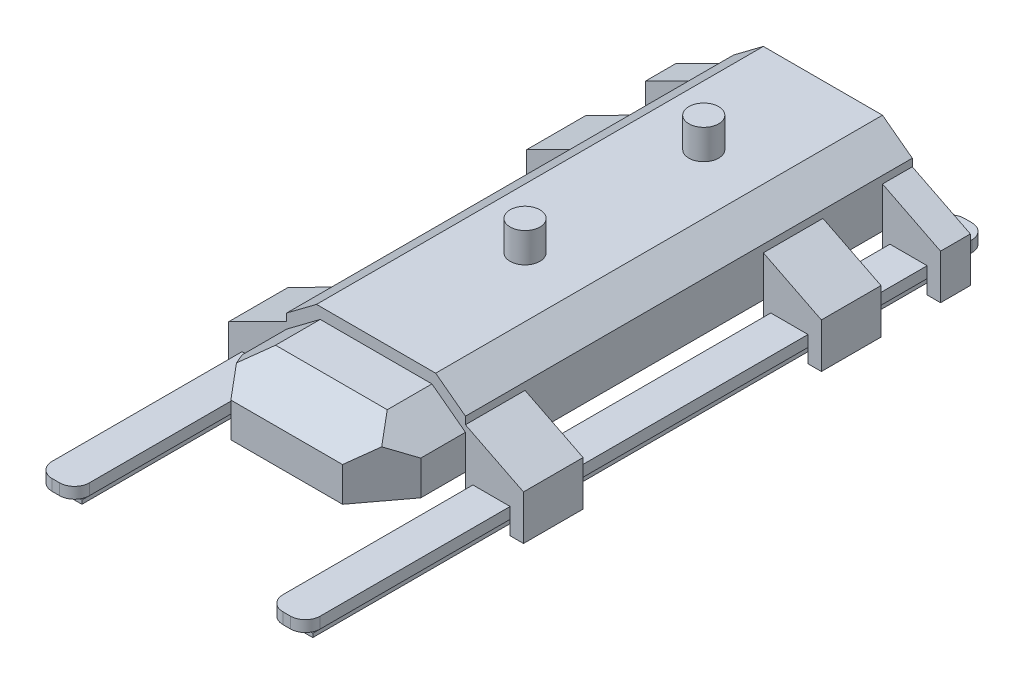
SolidWorks part; units mm, degrees
ref_plane "Front Plane" through (0, 0, 0) normal (0, 0, 1) x (1, 0, 0)
ref_plane "Top Plane" through (0, 0, 0) normal (0, 1, 0) x (1, 0, 0)
ref_plane "Right Plane" through (0, 0, 0) normal (1, 0, 0) x (0, 0, -1)
sketch "Sketch2" plane through (0, 0, 0) normal (0, 0, 1) x (1, 0, 0)
  line L0 (152.4, 0) -> (0, 0)
  line L1 (0, 0) -> (0, 120.65)
  line L2 (0, 120.65) -> (101.6, 120.65)
  line L3 (101.6, 120.65) -> (152.4, 82.55)
  line L4 (152.4, 82.55) -> (152.4, 69.85)
  line L5 (152.4, 0) -> (152.4, -50.8)
  line L6 (152.4, -50.8) -> (165.1, -50.8)
  line L7 (165.1, -50.8) -> (165.1, -12.7)
  line L8 (165.1, -12.7) -> (228.6, -12.7)
  line L9 (228.6, -12.7) -> (228.6, -56.0384)
  line L10 (228.6, -56.0384) -> (251.388, -56.0384)
  line L11 (251.388, -56.0384) -> (251.388, 20.1616)
  line L12 (251.388, 20.1616) -> (152.4, 69.85)
  dimension "D1" = 120.65
  dimension "D2" = 101.6
  dimension "D3" = 50.8
  dimension "D4" = 38.1
  dimension "D5" = 12.7
  dimension "D6" = 152.4
  dimension "D7" = 50.8
  dimension "D8" = 12.7
  dimension "D9" = 63.5
  dimension "D10" = 38.1
  dimension "D11" = 76.2
extrude "Boss-Extrude1" add sketch "Sketch2" along normal mid plane 762
sketch "Sketch3" plane through (0, 0, 0) normal (0, 1, 0) x (1, 0, 0)
  line L0 (152.4, -381) -> (152.4, 381) construction
  line L1 (152.4, -279.4) -> (251.388, -279.4)
  line L2 (152.4, -279.4) -> (152.4, 127)
  line L3 (152.4, 127) -> (251.388, 127)
  line L4 (251.388, -279.4) -> (251.388, 127)
  line L5 (251.388, -381) -> (251.388, 381) construction
  line L6 (251.388, -381) -> (152.4, -381) construction
  line L7 (152.4, 228.6) -> (251.388, 228.6)
  line L8 (152.4, 228.6) -> (152.4, 330.2)
  line L9 (152.4, 330.2) -> (251.388, 330.2)
  line L10 (251.388, 228.6) -> (251.388, 330.2)
  line L11 (251.388, 381) -> (152.4, 381) construction
  dimension "D1" = 101.6
  dimension "D2" = 50.8
  dimension "D3" = 101.6
  dimension "D4" = 101.6
extrude "Cut-Extrude1" cut sketch "Sketch3" against normal through all both and the other way through all
sketch "Sketch4" plane through (0, 0, 381) normal (0, 0, 1) x (1, 0, 0)
  line L0 (152.4, 0) -> (0, 0)
  line L1 (0, 0) -> (152.4, 0) construction
  line L2 (0, 0) -> (0, 101.6)
  line L3 (0, 120.65) -> (0, 0) construction
  line L4 (0, 101.6) -> (95.25, 101.6)
  line L5 (95.25, 101.6) -> (152.4, 58.7375)
  line L6 (152.4, 58.7375) -> (152.4, 0)
  line L7 (101.6, 120.65) -> (0, 120.65) construction
  line L8 (152.4, 82.55) -> (101.6, 120.65) construction
  line L9 (152.4, 0) -> (152.4, -50.8) construction
  dimension "D1" = 19.05
  dimension "D2" = 19.05
extrude "Boss-Extrude2" add sketch "Sketch4" along normal blind 152.4
sketch "Sketch6" plane through (0, 0, 0) normal (1, 0, 0) x (0, 0, -1)
  line L0 (-533.4, 101.6) -> (-533.4, 58.7375)
  line L1 (-533.4, 58.7375) -> (-457.2, 101.6)
  line L2 (-533.4, 101.6) -> (-381, 101.6) construction
  line L3 (-457.2, 101.6) -> (-533.4, 101.6)
extrude "Cut-Extrude2" cut sketch "Sketch6" against normal through all and the other way through all contours L3 L0 L1
sketch "Sketch7" plane through (0, 0, 0) normal (0, 1, 0) x (1, 0, 0)
  line L0 (152.4, -533.4) -> (152.4, -457.2)
  line L1 (152.4, -533.4) -> (152.4, -381) construction
  line L2 (152.4, -457.2) -> (95.25, -533.4)
  line L3 (152.4, -533.4) -> (0, -533.4) construction
  line L4 (95.25, -533.4) -> (152.4, -533.4)
extrude "Cut-Extrude3" cut sketch "Sketch7" against normal through all both and the other way through all
mirror "Mirror1" about plane through (0, 0, 0) normal (1, 0, 0) of bodies 105
sketch "Sketch8" plane through (0, 0, 0) normal (0, 0, 1) x (1, 0, 0)
  line L0 (-165.1, -50.8) -> (-165.1, -12.7) construction
  line L1 (-228.6, -12.7) -> (-165.1, -12.7)
  line L2 (-228.6, -12.7) -> (-228.6, -31.75)
  line L3 (-228.6, -31.75) -> (-165.1, -31.75)
  line L4 (-165.1, -12.7) -> (-165.1, -31.75)
  line L5 (228.6, -12.7) -> (228.6, -56.0384) construction
  line L6 (165.1, -12.7) -> (228.6, -12.7)
  line L7 (165.1, -12.7) -> (165.1, -31.75)
  line L8 (165.1, -31.75) -> (228.6, -31.75)
  line L9 (228.6, -12.7) -> (228.6, -31.75)
  dimension "D1" = 19.05
extrude "Boss-Extrude3" add sketch "Sketch8" along normal offset from surface 196.85 and the other way offset from surface (431.8 mm away) 50.8 up to face at (0, 29.3687, 533.4) offset beyond the face yes other way up to face at (0, 4.9213, -381)
fillet "Fillet1" radius 25.4 8 edges at (-228.6, -22.225, -431.8) (-165.1, -22.225, -431.8) (165.1, -22.225, -431.8) (228.6, -22.225, -431.8) (-228.6, -22.225, 730.25) (-165.1, -22.225, 730.25) (165.1, -22.225, 730.25) (228.6, -22.225, 730.25)
sketch "Sketch9" plane through (0, 0, 0) normal (0, 0, 1) x (1, 0, 0)
  line L0 (196.85, -31.75) -> (196.85, -50.8) construction
  line L1 (203.2, -31.75) -> (190.5, -31.75) construction
  line L2 (177.8, -50.8) -> (215.9, -50.8)
  line L3 (215.9, -50.8) -> (215.9, -44.45)
  line L4 (215.9, -44.45) -> (209.55, -44.45)
  line L5 (209.55, -44.45) -> (209.55, -31.75)
  line L6 (203.2, -31.75) -> (228.6, -31.75) construction
  line L7 (209.55, -31.75) -> (184.15, -31.75)
  line L8 (177.8, -50.8) -> (177.8, -44.45)
  line L9 (177.8, -44.45) -> (184.15, -44.45)
  line L10 (184.15, -44.45) -> (184.15, -31.75)
  line L11 (0, 0) -> (0, -74.2629) construction
  line L12 (-184.15, -44.45) -> (-184.15, -31.75)
  line L13 (-177.8, -44.45) -> (-184.15, -44.45)
  line L14 (-177.8, -50.8) -> (-177.8, -44.45)
  line L15 (-209.55, -31.75) -> (-184.15, -31.75)
  line L16 (-209.55, -44.45) -> (-209.55, -31.75)
  line L17 (-215.9, -44.45) -> (-209.55, -44.45)
  line L18 (-215.9, -50.8) -> (-215.9, -44.45)
  line L19 (-177.8, -50.8) -> (-215.9, -50.8)
  line L20 (-196.85, -31.75) -> (-196.85, -50.8) construction
  dimension "D1" = 12.7
  dimension "D2" = 6.35
  dimension "D3" = 19.05
  dimension "D4" = 12.7
extrude "Boss-Extrude4" add sketch "Sketch9" along normal offset from surface 25.4 and the other way offset from surface (406.4 mm away) 25.4 up to face at (196.85, -22.225, 730.25) other way up to face at (196.85, -22.225, -431.8)
sketch "Sketch10" plane through (0, 120.65, 0) normal (0, 1, 0) x (1, 0, 0)
  line L0 (0, 381) -> (0, -381) construction
  line L1 (101.6, 381) -> (-101.6, 381) construction
  line L2 (101.6, -381) -> (-101.6, -381) construction
  circle A0 centre (0, 177.8) radius 25.4
  circle A1 centre (0, -127) radius 25.4
  dimension "D1" = 50.8
  dimension "D2" = 254
  dimension "D3" = 304.8
extrude "Boss-Extrude5" add sketch "Sketch10" along normal blind 50.8
